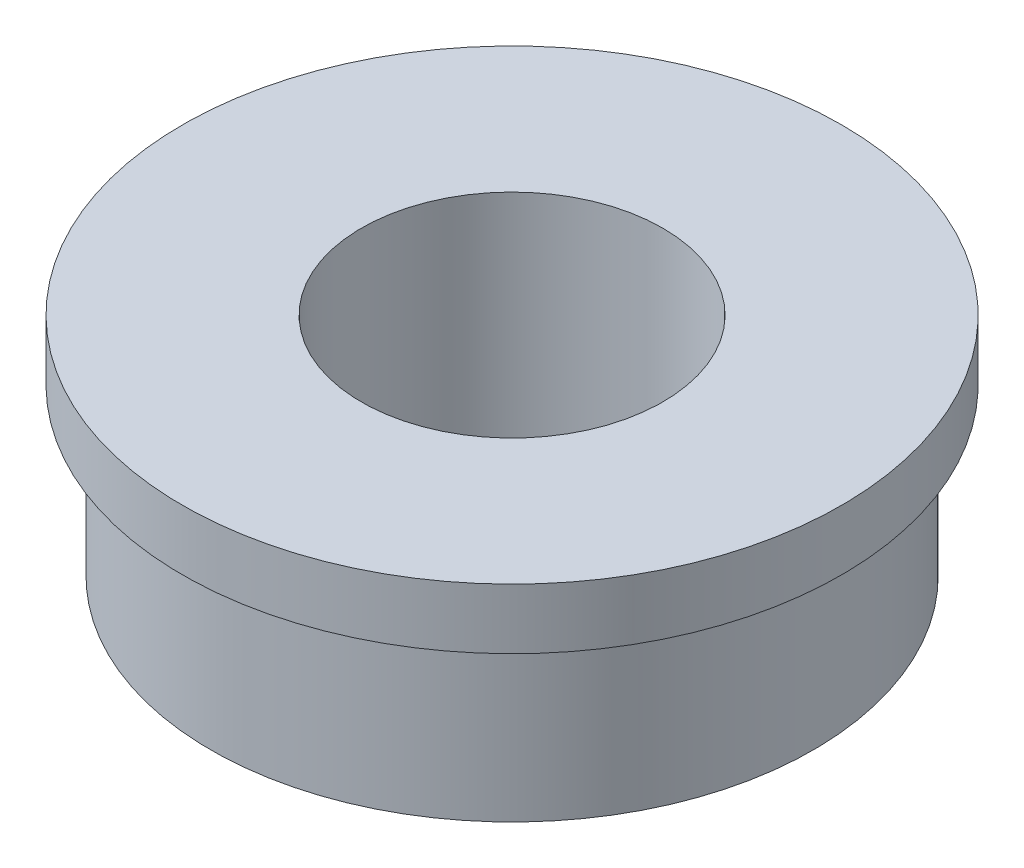
SolidWorks part; units mm, degrees
ref_plane "Front" through (0, 0, 0) normal (0, 0, 1) x (1, 0, 0)
ref_plane "Top" through (0, 0, 0) normal (0, 1, 0) x (1, 0, 0)
ref_plane "Right" through (0, 0, 0) normal (1, 0, 0) x (0, 0, -1)
sketch "Sketch1" plane through (0, 0, 0) normal (1, 0, 0) x (0, 0, -1)
  line L0 (3.175, 0) -> (6.35, 0)
  line L1 (6.35, 0) -> (6.35, 3.4925)
  line L2 (6.35, 3.4925) -> (6.9453, 3.4925)
  line L3 (6.9453, 3.4925) -> (6.9453, 4.7625)
  line L4 (6.9453, 4.7625) -> (3.175, 4.7625)
  line L6 (3.175, 4.7625) -> (3.175, 0)
  line L7 (0, 0) -> (0, 24.3656) construction
  dimension "D1" = 3.175
  dimension "D2" = 6.35
  dimension "D3" = 4.7625
  dimension "D4" = 6.9453
  dimension "D5" = 1.27
revolve "Revolve1" add sketch "Sketch1" angle 360 about L7
